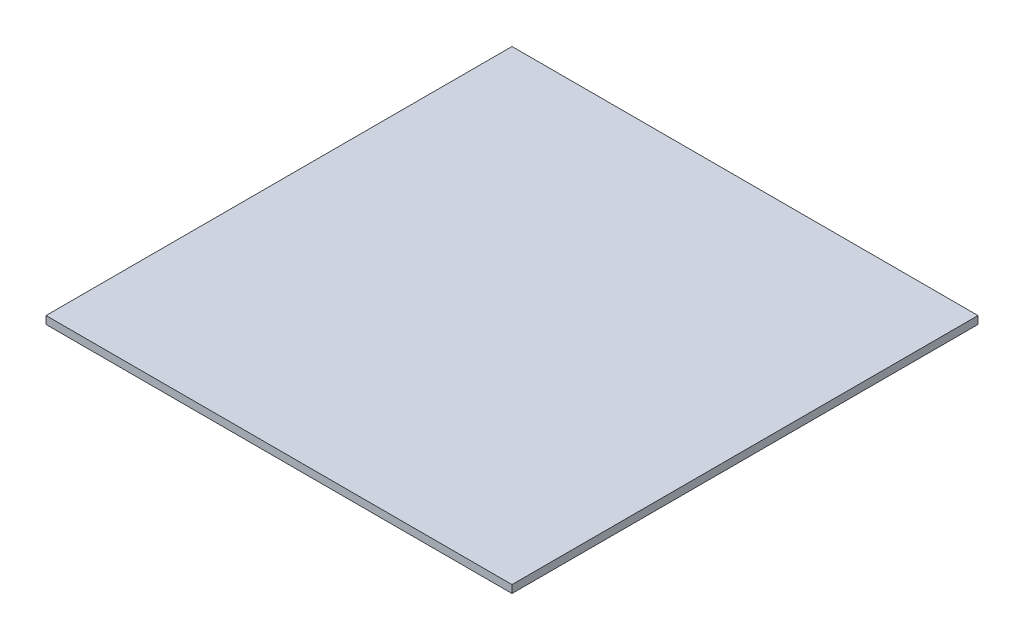
SolidWorks part; units mm, degrees
ref_plane "Front Plane" through (0, 0, 0) normal (0, 0, 1) x (1, 0, 0)
ref_plane "Top Plane" through (0, 0, 0) normal (0, 1, 0) x (1, 0, 0)
ref_plane "Right Plane" through (0, 0, 0) normal (1, 0, 0) x (0, 0, -1)
sketch3d "reference sketch"
  line L8 (-33.9558, -5, 152) -> (-33.9558, 145, 152)
  line L9 (-33.9558, 145, 152) -> (-33.9558, 145, -152.8)
  line L10 (-33.9558, 145, -152.8) -> (-33.9558, -5, -152.8)
  line L11 (-33.9558, -5, -152.8) -> (-33.9558, -5, 152)
sketch "Sketch1" plane through (0, 0, 0) normal (0, 1, 0) x (1, 0, 0)
  line L1 (-150, 150) -> (150, 150)
  line L2 (-150, 150) -> (-150, -150)
  line L3 (-150, -150) -> (150, -150)
  line L4 (150, 150) -> (150, -150)
  point P4 (0, 150)
  point P6 (-150, 0)
  dimension "D1" = 300
extrude "Boss-Extrude1" add sketch "Sketch1" along normal blind 5
ref_plane "Plane1" through (0, 0, 75) normal (0, 0, 1) x (1, 0, 0)
ref_plane "Plane2" through (0, 0, -75) normal (0, 0, -1) x (-1, 0, 0)
sketch "Sketch3" plane through (0, 0, 75) normal (0, 0, 1) x (1, 0, 0)
  line L0 (-80, 41.6164) -> (-107.5003, 5)
  line L1 (-150, 5) -> (150, 5) construction
  line L2 (-110.6095, 125.7154) -> (-72.1323, 20)
  line L3 (-33.9558, 145) -> (-33.9558, -5) construction
  dimension "D1" = 150
  dimension "D2" = 112.5
  dimension "D3" = 70
  dimension "D4" = 80
  dimension "D5" = 15
sketch "Sketch5" plane through (0, 0, -75) normal (0, 0, -1) x (-1, 0, 0)
  line L0 (110.6095, 125.7154) -> (72.1323, 20) construction
  line L1 (80, 41.6164) -> (107.5003, 5) construction
  line L2 (110.6095, 125.7154) -> (72.1323, 20)
  line L3 (80, 41.6164) -> (107.5003, 5)
equation "\"D2@Sketch3\"=\"D1@Sketch3\"*.75"
